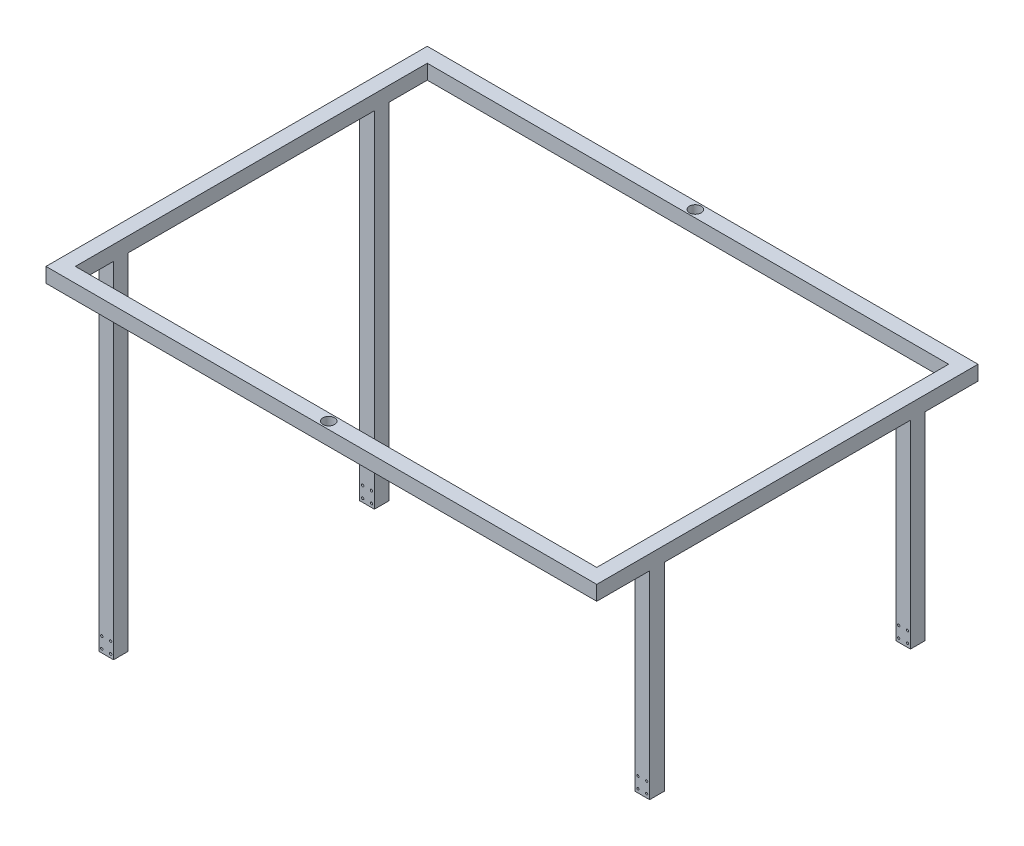
SolidWorks part; units mm, degrees
material "6061 合金"
ref_plane "前视基准面" through (0, 0, 0) normal (0, 0, 1) x (1, 0, 0)
ref_plane "上视基准面" through (0, 0, 0) normal (0, 1, 0) x (1, 0, 0)
ref_plane "右视基准面" through (0, 0, 0) normal (1, 0, 0) x (0, 0, -1)
sketch "草图1" plane through (0, 0, 0) normal (0, 1, 0) x (1, 0, 0)
  line L1 (-400.3658, 234.4582) -> (349.6342, 234.4582)
  line L2 (-400.3658, 234.4582) -> (-400.3658, -284.7418)
  line L3 (-400.3658, -284.7418) -> (349.6342, -284.7418)
  line L4 (349.6342, 234.4582) -> (349.6342, -284.7418)
  line L5 (329.6342, 214.4582) -> (-380.3658, 214.4582)
  line L6 (329.6342, 214.4582) -> (329.6342, -264.7418)
  line L7 (329.6342, -264.7418) -> (-380.3658, -264.7418)
  line L8 (-380.3658, 214.4582) -> (-380.3658, -264.7418)
  dimension "D1" = 750
  dimension "D2" = 519.2
  dimension "D3" = 20
  dimension "D4" = 20
  dimension "D5" = 20
  dimension "D6" = 20
extrude "凸台-拉伸1" add sketch "草图1" along normal blind 20
sketch "草图2" plane through (0, 0, 0) normal (0, -1, 0) x (1, 0, 0)
  line L0 (-400.3658, -234.4582) -> (-400.3658, 284.7418) construction
  line L5 (-380.3658, -214.4582) -> (-380.3658, 264.7418) construction
  line L6 (-400.3658, 284.7418) -> (349.6342, 284.7418) construction
  line L12 (-400.3658, 212.7418) -> (-380.3658, 212.7418)
  line L13 (-400.3658, 212.7418) -> (-400.3658, 192.7418)
  line L14 (-400.3658, 192.7418) -> (-380.3658, 192.7418)
  line L15 (-380.3658, 212.7418) -> (-380.3658, 192.7418)
  dimension "D6" = 20
  dimension "D7" = 72
extrude "凸台-拉伸2" add sketch "草图2" along normal blind 470
sketch "草图4" plane through (0, 0, 212.7418) normal (0, 0, 1) x (1, 0, 0)
  line L1 (-400.3658, -470) -> (-400.3658, 0) construction
  line L3 (-380.3658, -470) -> (-400.3658, -470) construction
  line L4 (-380.3658, -470) -> (-380.3658, 0) construction
  circle A0 centre (-396.3658, -465) radius 1.6
  circle A1 centre (-384.3658, -465) radius 1.6
  circle A2 centre (-396.3658, -450) radius 1.6
  circle A3 centre (-384.3658, -450) radius 1.6
  dimension "D1" = 4
  dimension "D3" = 12
  dimension "D5" = 15
  dimension "D6" = 12
  dimension "D2" = 5
  dimension "D7" = 3.2
  dimension "D8" = 4
  dimension "D9" = 5
  dimension "D4" = 15
ref_plane "基准面1" through (0, 0, 25.1418) normal (0, 0, 1) x (1, 0, 0)
sketch "草图6" plane through (0, 0, 0) normal (0, -1, 0) x (1, 0, 0)
  line L0 (349.6342, 284.7418) -> (349.6342, -234.4582) construction
  line L5 (329.6342, 264.7418) -> (329.6342, -214.4582) construction
  line L6 (349.6342, -234.4582) -> (-400.3658, -234.4582) construction
  line L12 (329.6342, -142.4582) -> (349.6342, -142.4582)
  line L13 (329.6342, -142.4582) -> (329.6342, -162.4582)
  line L14 (329.6342, -162.4582) -> (349.6342, -162.4582)
  line L15 (349.6342, -142.4582) -> (349.6342, -162.4582)
  dimension "D5" = 20
  dimension "D7" = 72
extrude "凸台-拉伸4" add sketch "草图6" along normal blind 270
sketch "草图7" plane through (0, 0, -162.4582) normal (0, 0, -1) x (-1, 0, 0)
  line L2 (-329.6342, -270) -> (-349.6342, -270) construction
  line L3 (-349.6342, -270) -> (-349.6342, 0) construction
  circle A0 centre (-345.6342, -265) radius 1.5
  circle A1 centre (-333.6342, -265) radius 1.5
  circle A2 centre (-345.6342, -250) radius 1.5
  circle A3 centre (-333.6342, -250) radius 1.5
  dimension "D1" = 5
  dimension "D2" = 4
  dimension "D4" = 15
  dimension "D5" = 4
  dimension "D6" = 12
  dimension "D7" = 15
  dimension "D8" = 5
  dimension "D3" = 12
extrude "Extrude1" cut sketch "草图4" against normal blind 30
extrude "Extrude2" cut sketch "草图7" against normal blind 30
mirror "Mirror1" about plane through (0, 0, 25.1418) normal (0, 0, 1) of "Extrude2", "Extrude1", "凸台-拉伸4", "凸台-拉伸2"
sketch "Sketch1" plane through (0, 20, 0) normal (0, 1, 0) x (1, 0, 0)
  line L0 (-25.3658, 234.4582) -> (-25.3658, -284.7418) construction
  line L1 (349.6342, 234.4582) -> (-400.3658, 234.4582) construction
  line L2 (-400.3658, -284.7418) -> (349.6342, -284.7418) construction
  circle A0 centre (-25.3658, 224.4582) radius 8
  circle A1 centre (-25.3658, -274.7418) radius 8
  point P8 (-25.3658, 224.5695)
  point P11 (-25.3658, -272.6009)
  dimension "D1" = 16
  dimension "D2" = 10
  dimension "D3" = 16
  dimension "D4" = 10
extrude "Extrude3" cut sketch "Sketch1" against normal blind 20
